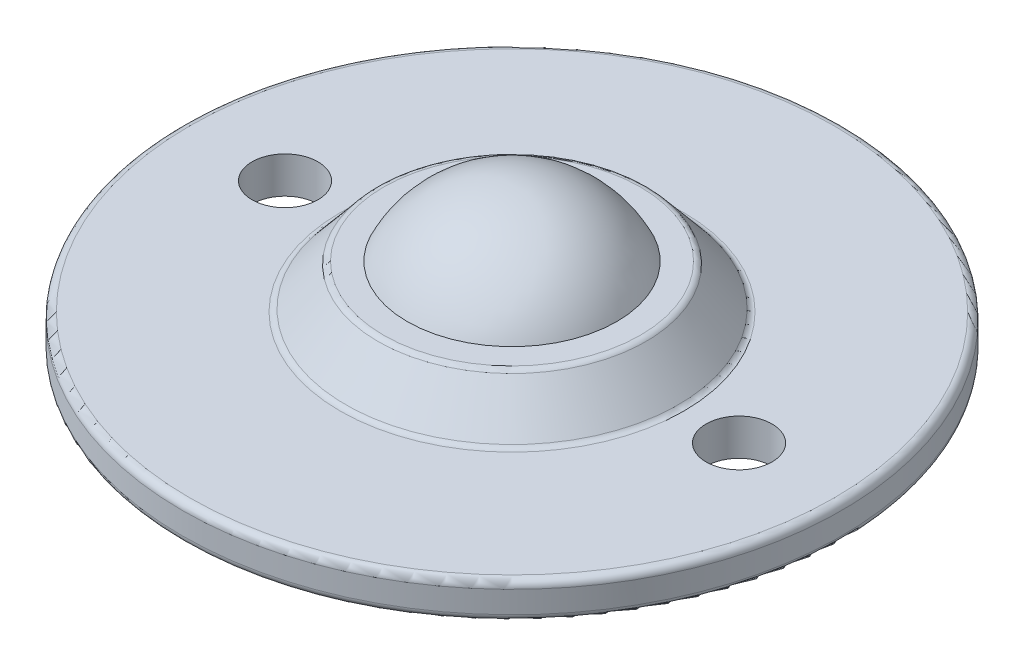
SolidWorks part; units mm, degrees
ref_plane "Front Plane" through (0, 0, 0) normal (0, 0, 1) x (1, 0, 0)
ref_plane "Top Plane" through (0, 0, 0) normal (0, 1, 0) x (1, 0, 0)
ref_plane "Right Plane" through (0, 0, 0) normal (1, 0, 0) x (0, 0, -1)
sketch "Sketch2" plane through (0, 0, 0) normal (1, 0, 0) x (0, 0, -1)
  line L0 (0, 7.9375) -> (0, -11.0625)
  line L1 (13, -2.0625) -> (22.5, -2.0625)
  line L2 (22.5, -2.0625) -> (22.5, 0.4375)
  line L3 (22.5, 0.4375) -> (11.5, 0.4375)
  line L4 (7.1545, 3.4375) -> (9, 3.4375)
  line L5 (9, 3.4375) -> (11.5, 0.4375)
  circle A0 centre (0, 0) radius 7.9375 construction
  arc A4 (0, 7.9375) -> (7.1545, 3.4375) centre (0, 0) cw
  arc A6 (0, -11.0625) -> (10.3545, -3.894) centre (0, 0) ccw
  arc A7 (13, -2.0625) -> (10.3545, -3.894) centre (13, -4.8889) ccw
  dimension "D1" = 15.875
  dimension "D2" = 11.5
  dimension "D3" = 13
  dimension "D4" = 22.5
  dimension "D5" = 3
  dimension "D6" = 19
  dimension "D7" = 2.5
  dimension "D8" = 9
  dimension "D9" = 9
revolve "Revolve1" add sketch "Sketch2" angle 360 about L0
sketch "Sketch3" plane through (0, 0.4375, 0) normal (0, 1, 0) x (1, 0, 0)
  line L0 (0, 0) -> (15.5, 0) construction
  line L1 (0, 0) -> (-15.5, 0) construction
  circle A0 centre (-15.5, 0) radius 2.25
  circle A1 centre (15.5, 0) radius 2.25
  dimension "D2" = 4.5
  dimension "D1" = 31
extrude "Cut-Extrude1" cut sketch "Sketch3" against normal through all
fillet "Fillet1" radius 0.5 4 edges at (0, 3.4375, 9) (0, 0.4375, 11.5) (0, -2.0625, 22.5) (0, 0.4375, 22.5)
